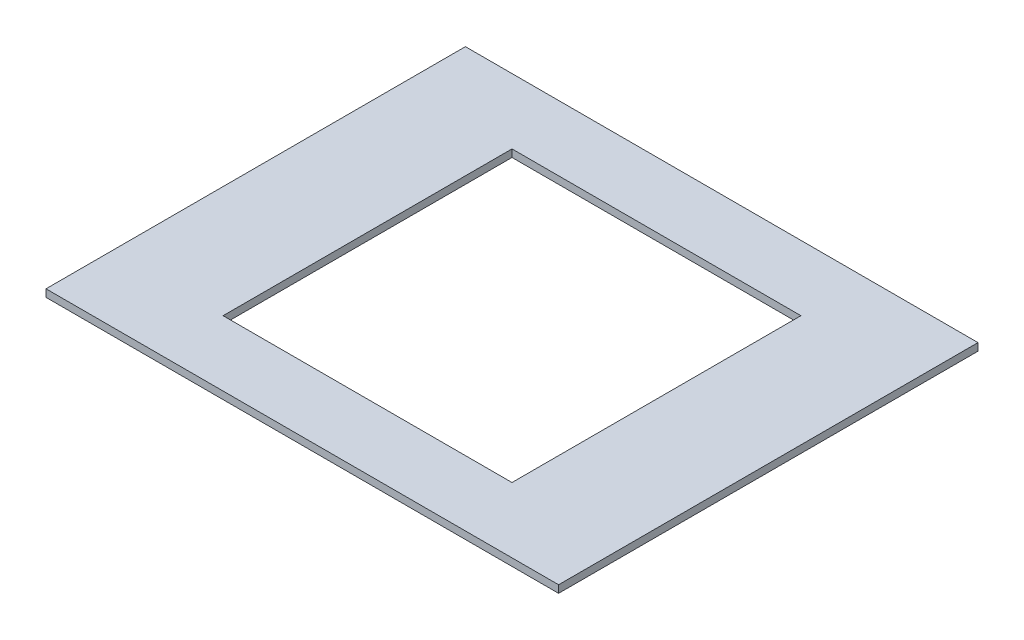
SolidWorks part; units mm, degrees
ref_plane "Front" through (0, 0, 0) normal (0, 0, 1) x (1, 0, 0)
ref_plane "Top" through (0, 0, 0) normal (0, 1, 0) x (1, 0, 0)
ref_plane "Right" through (0, 0, 0) normal (1, 0, 0) x (0, 0, -1)
sketch "Sketch1" plane through (0, 0, 0) normal (0, 1, 0) x (1, 0, 0)
  line L1 (0, 0) -> (110, 0)
  line L2 (0, 0) -> (0, 90)
  line L3 (0, 90) -> (110, 90)
  line L4 (110, 0) -> (110, 90)
  dimension "D1" = 110
  dimension "D2" = 90
extrude "Boss-Extrude1" add sketch "Sketch1" along normal blind 1.6
sketch "Sketch2" plane through (0, 1.6, 0) normal (0, 1, 0) x (1, 0, 0)
  line L22 (55, 76) -> (86, 76)
  line L23 (86, 45) -> (86, 76)
  line L26 (55, 14) -> (86, 14)
  line L27 (86, 45) -> (86, 14)
  line L30 (55, 76) -> (24, 76)
  line L31 (24, 45) -> (24, 76)
  line L34 (55, 14) -> (24, 14)
  line L35 (24, 45) -> (24, 14)
  dimension "D1" = 31
  dimension "D2" = 31
  dimension "D3" = 31
  dimension "D4" = 31
extrude "Cut-Extrude1" cut sketch "Sketch2" against normal blind 1.6
